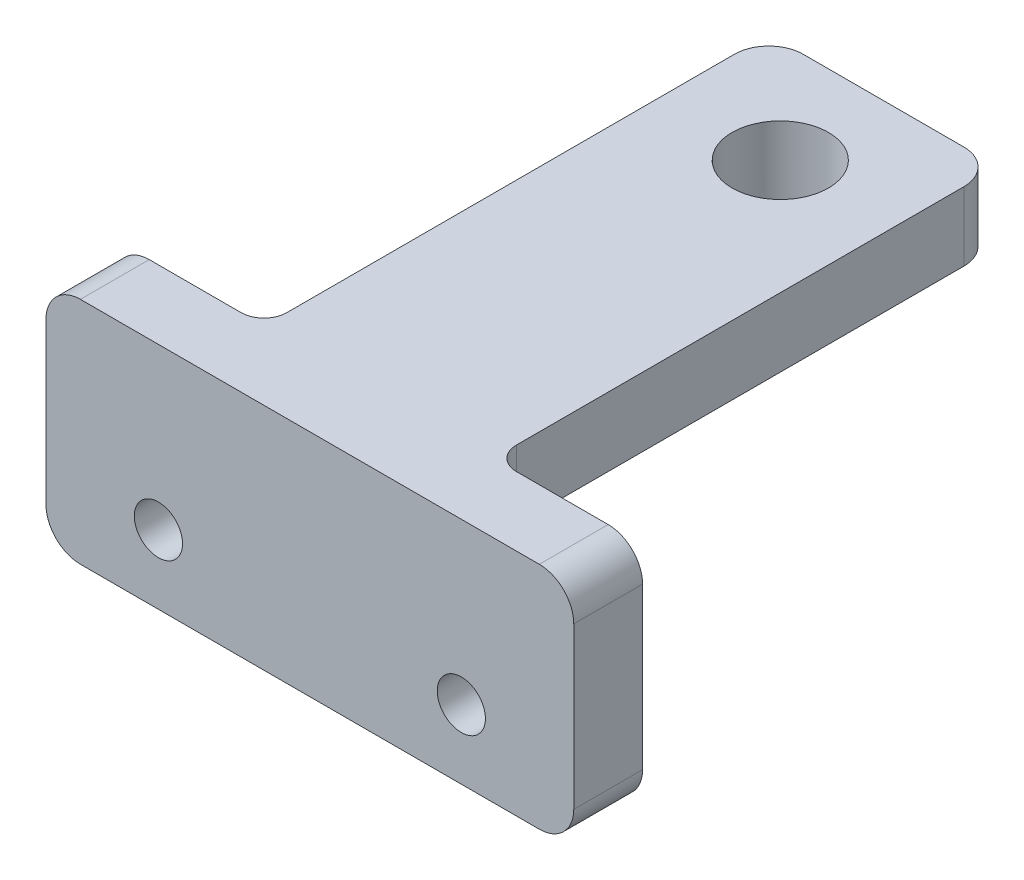
SolidWorks part; units mm, degrees
ref_plane "Front Plane" through (0, 0, 0) normal (0, 0, 1) x (1, 0, 0)
ref_plane "Top Plane" through (0, 0, 0) normal (0, 1, 0) x (1, 0, 0)
ref_plane "Right Plane" through (0, 0, 0) normal (1, 0, 0) x (0, 0, -1)
sketch "Sketch2" plane through (0, 0, 0) normal (0, 0, 1) x (1, 0, 0)
  line L0 (4.9, 3) -> (18.1, 3) construction
  line L1 (0, 0) -> (23, 0)
  line L2 (0, 0) -> (0, 10)
  line L3 (0, 10) -> (23, 10)
  line L4 (23, 0) -> (23, 10)
  circle A0 centre (4.9, 3) radius 1.05
  circle A1 centre (18.1, 3) radius 1.05
  point P9 (0, 0)
  point P10 (11.5, 3)
  point P11 (11.5, 0)
  dimension "D3" = 2.1
  dimension "D4" = 2.1
  dimension "D5" = 13.2
  dimension "D6" = 7
  dimension "D1" = 23
  dimension "D2" = 10
extrude "Boss-Extrude1" add sketch "Sketch2" along normal blind 3
sketch "Sketch3" plane through (0, 0, 3) normal (0, 0, 1) x (1, 0, 0)
  line L1 (6.5, 10) -> (16.5, 10)
  line L2 (6.5, 10) -> (6.5, 7)
  line L3 (6.5, 7) -> (16.5, 7)
  line L4 (16.5, 10) -> (16.5, 7)
  line L5 (23, 10) -> (0, 10) construction
  point P7 (11.5, 10)
  point P8 (11.5, 10)
  dimension "D1" = 3
  dimension "D2" = 10
extrude "Boss-Extrude2" add sketch "Sketch3" against normal blind 25
sketch "Sketch4" plane through (0, 10, 0) normal (0, 1, 0) x (1, 0, 0)
  line L0 (16.5, 22) -> (6.5, 22) construction
  circle A0 centre (11.5, 17.5) radius 2.1
  point P4 (11.5, 22)
  dimension "D1" = 4.2
  dimension "D2" = 4.5
extrude "Cut-Extrude1" cut sketch "Sketch4" against normal through all
fillet "Fillet1" radius 1.5 6 edges at (0, 0, 1.5) (23, 0, 1.5) (23, 10, 1.5) (0, 10, 1.5) (6.5, 8.5, -22) (16.5, 8.5, -22)
fillet "Fillet2" radius 1 3 edges at (11.5, 7, 0) (6.5, 8.5, 0) (16.5, 8.5, 0)
